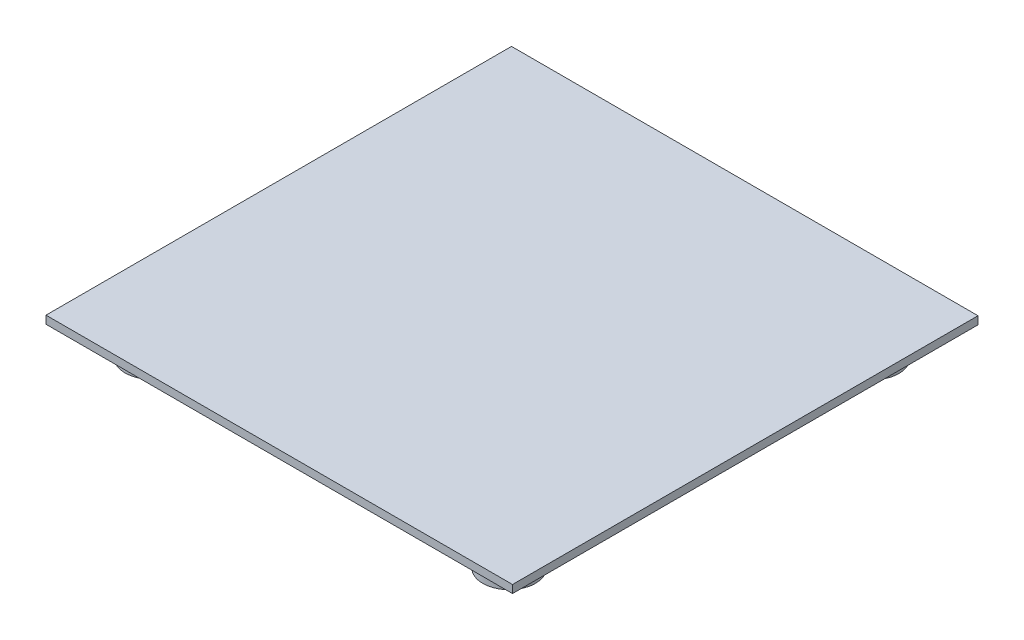
SolidWorks part; units mm, degrees
ref_plane "Front Plane" through (0, 0, 0) normal (0, 0, 1) x (1, 0, 0)
ref_plane "Top Plane" through (0, 0, 0) normal (0, 1, 0) x (1, 0, 0)
ref_plane "Right Plane" through (0, 0, 0) normal (1, 0, 0) x (0, 0, -1)
sketch "Sketch2" plane through (0, 0, 0) normal (0, 1, 0) x (1, 0, 0)
  line L2 (0, 0) -> (176.9, 0)
  line L3 (0, 0) -> (0, -176.52)
  line L4 (0, -176.52) -> (176.9, -176.52)
  line L5 (176.9, 0) -> (176.9, -176.52)
  dimension "D1" = 176.9
  dimension "D2" = 176.52
extrude "Boss-Extrude1" add sketch "Sketch2" along normal blind 3
sketch "Sketch6" plane through (0, 0, 0) normal (0, -1, 0) x (1, 0, 0)
  circle A0 centre (20, 156.52) radius 10
  circle A1 centre (156.9, 20) radius 10
  circle A2 centre (20, 20) radius 10
  circle A3 centre (156.9, 157.8064) radius 10
extrude "Boss-Extrude4" add sketch "Sketch6" along normal blind 11
sketch "Sketch7" plane through (0, 3, 0) normal (0, 1, 0) x (1, 0, 0)
